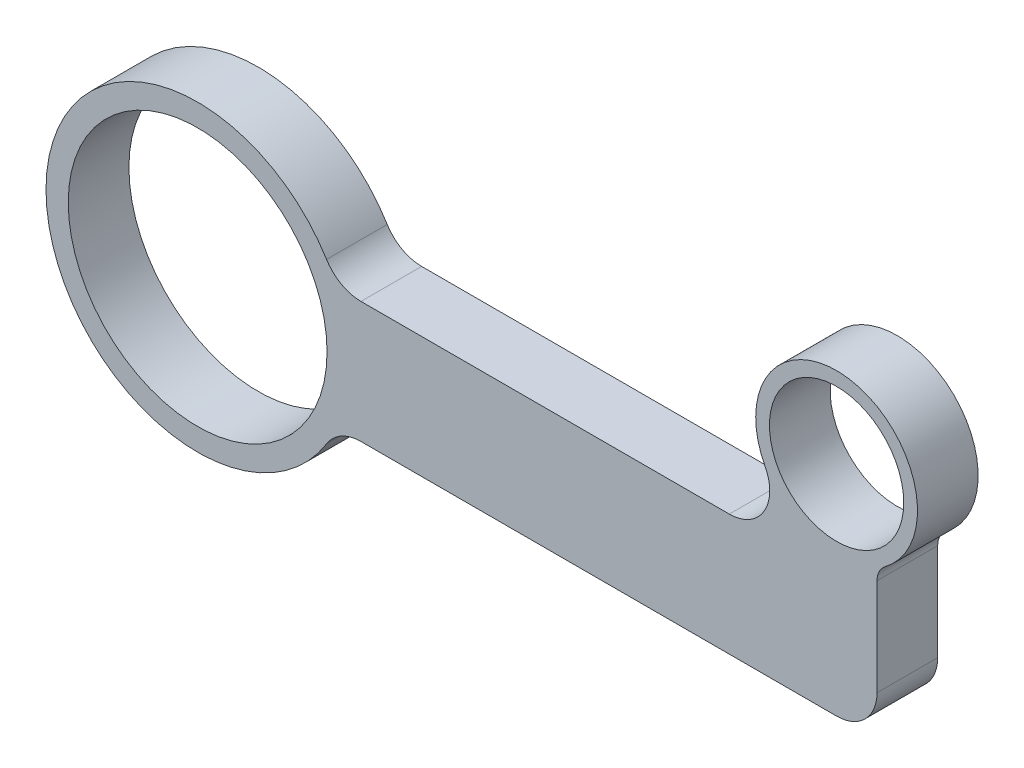
SolidWorks part; units mm, degrees
ref_plane "Front Plane" through (0, 0, 0) normal (0, 0, 1) x (1, 0, 0)
ref_plane "Top Plane" through (0, 0, 0) normal (0, 1, 0) x (1, 0, 0)
ref_plane "Right Plane" through (0, 0, 0) normal (1, 0, 0) x (0, 0, -1)
sketch "Sketch1" plane through (0, 0, 0) normal (0, 0, 1) x (1, 0, 0)
  line L0 (0, 224.84) -> (0, -226.6943) construction
  line L1 (-500.2409, 0) -> (494.4697, 0) construction
  line L2 (-49.0363, 19.05) -> (-12.7, 19.05)
  line L3 (-49.0363, -19.05) -> (12.7, -19.05)
  line L4 (0, 49.53) -> (192.2842, 49.53) construction
  line L7 (12.7, -19.05) -> (100.33, -19.05)
  line L8 (-201.93, 19.05) -> (-147.955, 19.05) construction
  line L10 (-201.93, 19.05) -> (-201.93, -19.05) construction
  line L12 (-201.93, -19.05) -> (-147.955, -19.05) construction
  line L13 (125.73, 62.23) -> (163.83, 62.23) construction
  line L14 (113.03, -6.35) -> (113.03, 24.13)
  line L15 (125.73, 36.83) -> (163.83, 36.83) construction
  line L16 (163.83, 62.23) -> (163.83, 36.83) construction
  line L18 (66.6331, 19.05) -> (-12.7, 19.05)
  line L19 (100.33, 49.53) -> (100.33, -43.4929) construction
  circle A0 centre (-100.33, 0) radius 40.64
  arc A1 (115.57, 29.21) -> (120.65, 34.29) centre (100.33, 49.53) ccw
  arc A2 (-59.835, 25.0658) -> (-142.3521, 22.4118) centre (-100.33, 0) ccw
  arc A3 (66.6331, 19.05) -> (77.8654, 37.6767) centre (66.6331, 31.75) ccw
  arc A4 (-59.835, 25.0658) -> (-49.0363, 19.05) centre (-49.0363, 31.75) ccw
  arc A5 (-59.835, -25.0658) -> (-49.0363, -19.05) centre (-49.0363, -31.75) cw
  arc A6 (-142.3521, -22.4118) -> (-59.835, -25.0658) centre (-100.33, 0) ccw
  arc A7 (-147.955, -19.05) -> (-142.3521, -22.4118) centre (-147.955, -25.4) cw construction
  circle A8 centre (100.33, 49.53) radius 21.082
  arc A9 (-142.3521, 22.4118) -> (-142.3521, -22.4118) centre (-100.33, 0) ccw
  arc A10 (120.65, 64.77) -> (120.65, 34.29) centre (100.33, 49.53) cw
  arc A11 (113.03, 24.13) -> (115.57, 29.21) centre (119.38, 24.13) cw
  arc A13 (-147.955, 19.05) -> (-142.3521, 22.4118) centre (-147.955, 25.4) ccw construction
  arc A15 (120.65, 64.77) -> (77.8654, 37.6767) centre (100.33, 49.53) ccw
  arc A16 (120.65, 34.29) -> (125.73, 36.83) centre (125.73, 30.48) cw construction
  arc A17 (125.73, 62.23) -> (120.65, 64.77) centre (125.73, 68.58) cw construction
  arc A19 (100.33, -19.05) -> (113.03, -6.35) centre (100.33, -6.35) ccw
  point P25 (-143.979, -19.05)
  point P32 (-147.955, 0)
  point P36 (125.73, 49.53)
  point P37 (113.03, 27.533)
  point P51 (122.327, 62.23)
  dimension "D1" = 81.28
  dimension "D2" = 95.25
  dimension "D4" = 6.35
  dimension "D5" = 12.7
  dimension "D7" = 12.7
  dimension "D8" = 200.66
  dimension "D11" = 42.164
  dimension "D14" = 6.35
  dimension "D17" = 6.35
  dimension "D22" = 12.7
  dimension "D6" = 50.8
  dimension "D3" = 38.1
  dimension "D9" = 49.53
  dimension "D13" = 100.33
  dimension "D15" = 38.1
  dimension "D16" = 101.6
  dimension "D18" = 63.5
  dimension "D19" = 25.4
extrude "Boss-Extrude1" add sketch "Sketch1" along normal blind 19.05
